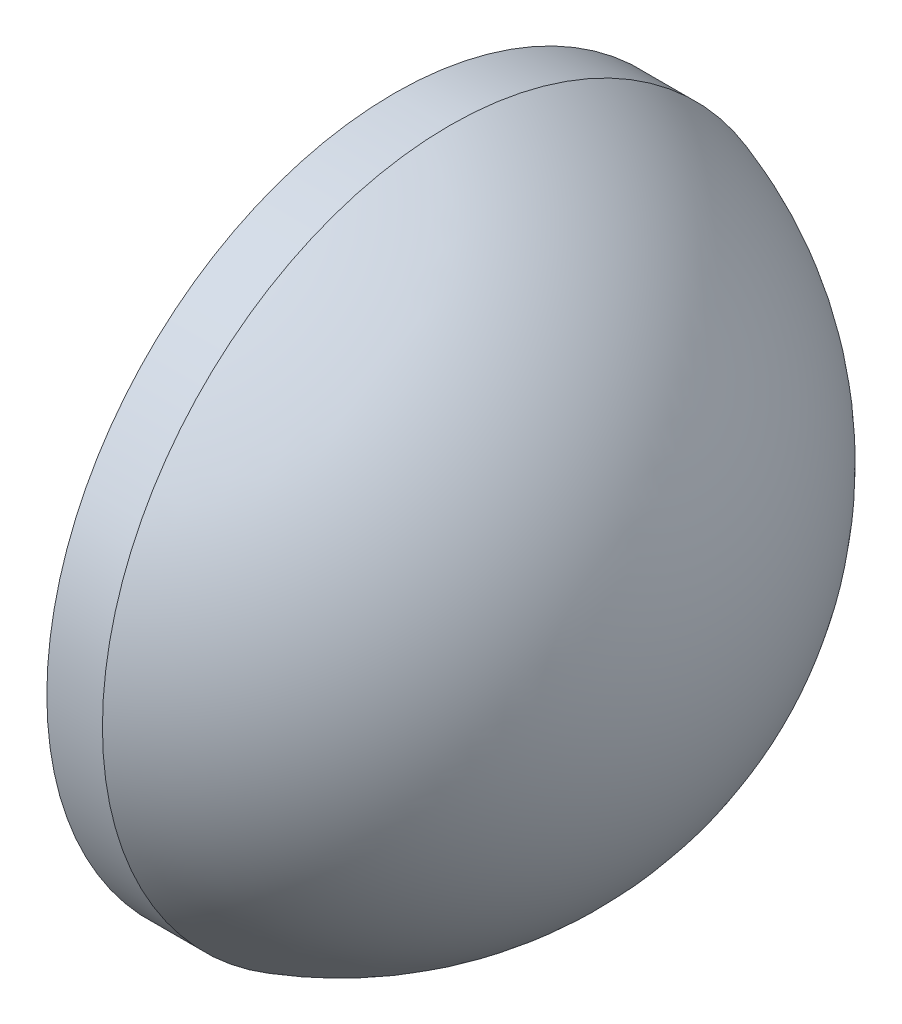
SolidWorks part; units mm, degrees
ref_plane "前视基准面" through (0, 0, 0) normal (0, 0, 1) x (1, 0, 0)
ref_plane "上视基准面" through (0, 0, 0) normal (0, 1, 0) x (1, 0, 0)
ref_plane "右视基准面" through (0, 0, 0) normal (1, 0, 0) x (0, 0, -1)
sketch "草图1" plane through (0, 0, 0) normal (0, 0, 1) x (1, 0, 0)
  line L0 (417.4229, 66.578) -> (432.8839, 66.578) construction
  line L1 (419.9279, 66.578) -> (419.9279, 79.078)
  line L2 (419.9279, 79.078) -> (421.9279, 79.078)
  line L3 (431.0879, 66.578) -> (419.9279, 66.578)
  arc A0 (431.0879, 66.578) -> (421.9279, 79.078) centre (417.979, 66.578) ccw
revolve "旋转1" add sketch "草图1" angle 360 about L0
